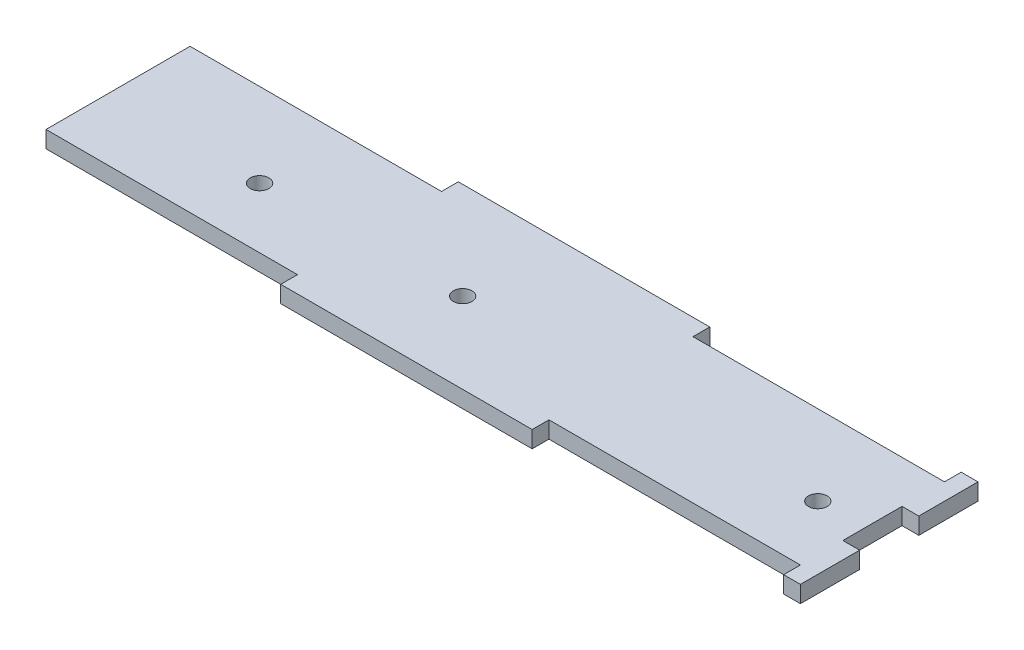
SolidWorks part; units mm, degrees
ref_plane "Front Plane" through (0, 0, 0) normal (0, 0, 1) x (1, 0, 0)
ref_plane "Top Plane" through (0, 0, 0) normal (0, 1, 0) x (1, 0, 0)
ref_plane "Right Plane" through (0, 0, 0) normal (1, 0, 0) x (0, 0, -1)
sketch "Sketch1" plane through (0, 0, 0) normal (0, 1, 0) x (1, 0, 0)
  line L2 (0, 0) -> (0, 15.2)
  line L6 (4, 2.8333) -> (4, 12.3667)
  line L8 (-117.5, 12.3667) -> (-117.5, 2.8333)
  line L11 (6.7, -6.7) -> (4, -6.7)
  line L12 (-111.5, -4) -> (-111.5, 19.2) construction
  line L17 (6.7, -6.7) -> (6.7, 2.8333)
  line L18 (0, 15.2) -> (-107.5, 15.2) construction
  line L19 (-107.5, 0) -> (-107.5, 15.2) construction
  line L20 (0, 0) -> (-107.5, 0) construction
  line L21 (-111.5, -4) -> (-117.5, -4) construction
  line L22 (4, -4) -> (-111.5, -4) construction
  line L23 (-117.5, -4) -> (-77, -4)
  line L25 (-120.2, 21.9) -> (-120.2, -6.7) construction
  line L28 (-36.5, -4) -> (4, -4)
  line L31 (-77, -4) -> (-77, -6.7)
  line L32 (-36.5, -4) -> (-36.5, -6.7)
  line L35 (-117.5, 19.2) -> (-117.5, -4) construction
  line L36 (-111.5, -6.7) -> (-120.2, -6.7) construction
  line L37 (6.7, -6.7) -> (-111.5, -6.7) construction
  line L39 (6.7, -6.7) -> (6.7, 21.9) construction
  line L40 (6.7, 12.3667) -> (6.7, 21.9)
  line L41 (6.7, 12.3667) -> (4, 12.3667)
  line L42 (6.7, 2.8333) -> (4, 2.8333)
  line L43 (4, -4) -> (4, -6.7)
  line L44 (4, 19.2) -> (4, 21.9)
  line L45 (4, -4) -> (4, 19.2) construction
  line L46 (-36.5, -6.7) -> (-77, -6.7)
  line L47 (4, 19.2) -> (-111.5, 19.2) construction
  line L48 (-111.5, 19.2) -> (-117.5, 19.2) construction
  line L49 (6.7, 21.9) -> (-111.5, 21.9) construction
  line L50 (-111.5, 21.9) -> (-120.2, 21.9) construction
  line L52 (6.7, 21.9) -> (4, 21.9)
  line L53 (-117.5, 19.2) -> (-117.5, 12.3667)
  line L54 (-36.5, 19.2) -> (4, 19.2)
  line L55 (-36.5, 19.2) -> (-36.5, 21.9)
  line L56 (-36.5, 21.9) -> (-77, 21.9)
  line L57 (-77, 19.2) -> (-77, 21.9)
  line L58 (-117.5, 19.2) -> (-77, 19.2)
  line L59 (-117.5, 2.8333) -> (-117.5, -4)
  circle A0 centre (-3.5, 6.3) radius 1.5
  circle A1 centre (-60.7, 6.3) radius 1.5
  circle A2 centre (-92.8, 5.7) radius 1.5
  point P7 (-12.4, 6.1)
  point P8 (-52.4, 6.1)
  point P9 (-34.4, 6.1)
  point P10 (-70.4, 6.1)
  point P11 (-88.4, 6.1)
  dimension "D3" = 12.4
  dimension "D9" = 60.7
  dimension "D5" = 34.4
  dimension "D6" = 52.4
  dimension "D7" = 70.4
  dimension "D8" = 88.4
  dimension "D14" = 96.8
  dimension "D11" = 4
  dimension "D15" = 2.7
extrude "Boss-Extrude1" add sketch "Sketch1" along normal blind 2.7
